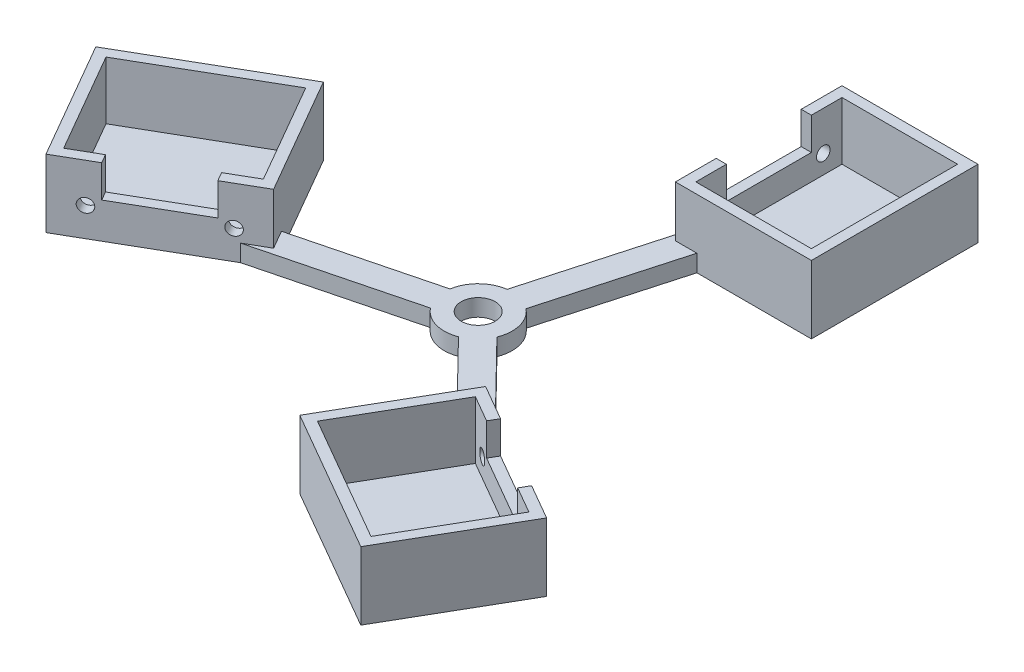
SolidWorks part; units mm, degrees
ref_plane "Front Plane" through (0, 0, 0) normal (0, 0, 1) x (1, 0, 0)
ref_plane "Top Plane" through (0, 0, 0) normal (0, 1, 0) x (1, 0, 0)
ref_plane "Right Plane" through (0, 0, 0) normal (1, 0, 0) x (0, 0, -1)
sketch "Sketch1" plane through (0, 0, 0) normal (0, 1, 0) x (1, 0, 0)
  line L7 (14, 93) -> (48, 93)
  line L8 (14, 93) -> (14, 50)
  line L9 (14, 50) -> (48, 50)
  line L10 (48, 93) -> (48, 50)
  point P4 (11, 96)
  point P5 (11, 47)
  point P6 (51, 47)
  point P8 (0, 0)
  point P10 (7.2222, -2.0222)
  point P12 (21.2222, 47.9778)
  dimension "D1" = 14
  dimension "D2" = 50
  dimension "D3" = 43
  dimension "D4" = 34
sketch "Sketch3" plane through (0, 0, 0) normal (0, 1, 0) x (1, 0, 0)
  line L4 (14, 93) -> (14, 50)
  line L5 (14, 50) -> (48, 50)
  line L6 (48, 50) -> (48, 93)
  line L7 (48, 93) -> (14, 93)
  line L8 (51, 96) -> (11, 96)
  line L9 (51, 47) -> (51, 96)
  line L10 (11, 47) -> (51, 47)
  line L11 (11, 96) -> (11, 47)
  line L12 (51, 96) -> (11, 96)
  line L13 (51, 47) -> (51, 96)
  line L14 (11, 47) -> (51, 47)
  line L15 (11, 96) -> (11, 47)
  dimension "D1" = 3
sketch "Sketch4" plane through (0, 0, 0) normal (0, 1, 0) x (1, 0, 0)
  line L0 (14, 50) -> (0, 0) construction
  line L1 (6.3231, 7.7472) -> (17.3138, 47)
  line L2 (-1.3807, 9.9042) -> (11, 54.1209)
  line L3 (11, 47) -> (11, 54.1209)
  line L4 (11, 47) -> (17.3138, 47)
  arc A0 (-1.3807, 9.9042) -> (6.3231, 7.7472) centre (0, 0) ccw
  point P1 (14, 50)
  dimension "D3" = 20
  dimension "D1" = 4
  dimension "D2" = 4
extrude "Boss-Extrude3" add sketch "Sketch4" along normal blind 5
extrude "Boss-Extrude4" add sketch "Sketch3" along normal blind 10.5
extrude "Boss-Extrude5" add sketch "Sketch1" along normal blind 3
sketch "Sketch7" plane through (0, 10.5, 0) normal (0, 1, 0) x (1, 0, 0)
  line L0 (14, 50) -> (14, 59)
  line L1 (14, 93) -> (14, 50) construction
  line L2 (14, 59) -> (11, 59)
  line L3 (11, 96) -> (11, 47) construction
  line L4 (11, 59) -> (11, 47)
  line L5 (11, 47) -> (51, 47)
  line L6 (51, 47) -> (51, 96)
  line L7 (51, 47) -> (51, 96) construction
  line L8 (48, 93) -> (48, 50)
  line L9 (48, 50) -> (48, 93) construction
  line L10 (48, 50) -> (14, 50)
  line L11 (48, 71.5) -> (51, 71.5) construction
  line L12 (48, 93) -> (14, 93)
  line L13 (11, 96) -> (51, 96)
  line L14 (11, 84) -> (11, 96)
  line L15 (14, 84) -> (11, 84)
  line L16 (14, 93) -> (14, 84)
  dimension "D1" = 9
extrude "Boss-Extrude6" add sketch "Sketch7" along normal blind 9.5
sketch "Sketch6" plane through (14, 0, 0) normal (1, 0, 0) x (0, 0, -1)
  line L0 (50, 3) -> (55.5, 3) construction
  line L1 (93, 3) -> (50, 3) construction
  line L2 (55.5, 3) -> (55.5, 8.5) construction
  line L3 (71.5, 3) -> (71.5, 10.5) construction
  line L4 (84, 10.5) -> (59, 10.5) construction
  circle A0 centre (55.5, 8.5) radius 2
  circle A1 centre (87.5, 8.5) radius 2
  dimension "D3" = 4
  dimension "D1" = 5.5
  dimension "D2" = 5.5
extrude "Cut-Extrude1" cut sketch "Sketch6" against normal up to next (3 mm away)
sketch "Sketch5" plane through (0, 0, 0) normal (0, 0, 1) x (1, 0, 0)
  line L0 (0, 0) -> (0, 51.3429) construction
pattern_circular "CirPattern1" count 3 over 360 about axis through (0, 0, 0) along (0, 1, 0) of "Boss-Extrude3", "Boss-Extrude5", "Boss-Extrude4", "Cut-Extrude1", "Boss-Extrude6"
sketch "Sketch8" plane through (0, 5, 0) normal (0, 1, 0) x (1, 0, 0)
  circle A0 centre (0, 0) radius 5
  dimension "D1" = 10
extrude "Cut-Extrude2" cut sketch "Sketch8" against normal blind 9.5
